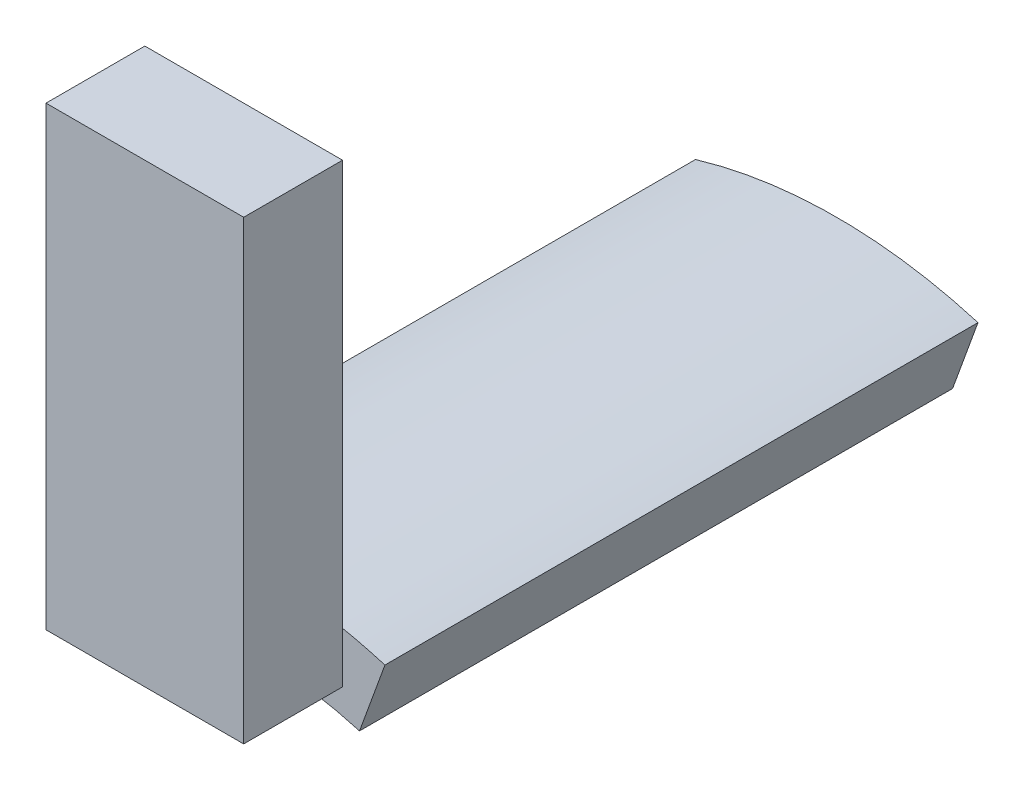
SolidWorks part; units mm, degrees
ref_plane "Plan1" through (0, 0, 0) normal (0, 0, 1) x (1, 0, 0)
ref_plane "Plan2" through (0, 0, 0) normal (0, 1, 0) x (1, 0, 0)
ref_plane "Plan3" through (0, 0, 0) normal (1, 0, 0) x (0, 0, -1)
sketch "Esquisse1" plane through (0, 0, 0) normal (0, 0, 1) x (1, 0, 0)
  line L2 (-1.4291, 4.7914) -> (-1.172, 4.0852)
  line L3 (1.172, 4.0852) -> (1.4291, 4.7914)
  line L4 (-1.4291, 4.7914) -> (-1.172, 4.0852)
  line L5 (1.172, 4.0852) -> (1.4291, 4.7914)
  arc A2 (1.4291, 4.7914) -> (-1.4291, 4.7914) centre (0, 0) ccw
  arc A3 (1.172, 4.0852) -> (-1.172, 4.0852) centre (0, 0) ccw
  arc A4 (1.4291, 4.7914) -> (-1.4291, 4.7914) centre (0, 0) ccw
  arc A5 (1.172, 4.0852) -> (-1.172, 4.0852) centre (0, 0) ccw
  dimension "D1" = 0
extrude "Base-Extrusion" add sketch "Esquisse1" along normal up to surface (6 mm away)
sketch "Esquisse2" plane through (0, 0, 6) normal (0, 0, 1) x (1, 0, 0)
  line L0 (0, 0) -> (0, 8.0522) construction
  line L1 (-1, 4.3852) -> (1, 4.3852)
  line L2 (-1, 4.3852) -> (-1, 9)
  line L3 (-1, 9) -> (1, 9)
  line L4 (1, 4.3852) -> (1, 9)
  dimension "D1" = 0.3
  dimension "D2" = 2
  dimension "D3" = 9
extrude "Boss.-Extru.1" add sketch "Esquisse2" along normal blind 1
